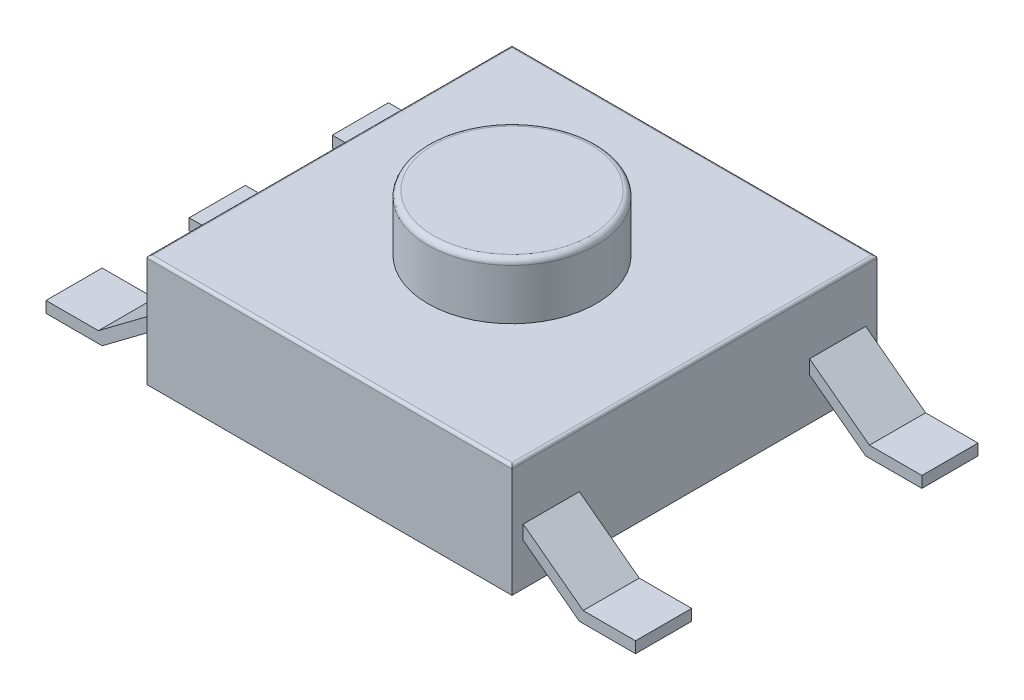
SolidWorks part; units mm, degrees
ref_plane "Front" through (0, 0, 0) normal (0, 0, 1) x (1, 0, 0)
ref_plane "Top" through (0, 0, 0) normal (0, 1, 0) x (1, 0, 0)
ref_plane "Right" through (0, 0, 0) normal (1, 0, 0) x (0, 0, -1)
sketch "Sketch1" plane through (0, 0, 0) normal (0, 1, 0) x (1, 0, 0)
  line L1 (0, 0) -> (6.5, 0)
  line L2 (0, 0) -> (0, 6.5)
  line L3 (0, 6.5) -> (6.5, 6.5)
  line L4 (6.5, 0) -> (6.5, 6.5)
  dimension "D1" = 6.5
extrude "Boss-Extrude1" add sketch "Sketch1" along normal blind 2
sketch "Sketch2" plane through (0, 2, 0) normal (0, 1, 0) x (1, 0, 0)
  line L0 (0, 0) -> (6.5, 6.5) construction
  circle A0 centre (3.25, 3.25) radius 1.5
  dimension "D1" = 3
extrude "Boss-Extrude2" add sketch "Sketch2" along normal blind 1
fillet "Fillet1" radius 0.1 1 edges at (3.25, 3, -1.75)
fillet "Fillet2" radius 0.05 4 edges at (3.25, 2, 0) (6.5, 2, -3.25) (3.25, 2, -6.5) (0, 2, -3.25)
sketch "Sketch3" plane through (0, 0, 0) normal (0, 0, 1) x (1, 0, 0)
  line L0 (6.5, 1) -> (7.5667, 0.2)
  line L1 (6.5, 1.95) -> (6.5, 0) construction
  line L2 (7.5667, 0.2) -> (8.5, 0.2)
  line L3 (8.5, 0.2) -> (8.5, 0)
  line L4 (8.5, 0) -> (7.5, 0)
  line L5 (7.5, 0) -> (6.5, 0.75)
  line L6 (3.25, 1.95) -> (3.25, 0) construction
  line L7 (6.5, 1.95) -> (0, 1.95) construction
  line L8 (0, 0) -> (6.5, 0) construction
  line L9 (-2, 0) -> (-1, 0)
  line L10 (-2, 0.2) -> (-2, 0)
  line L11 (-1.0667, 0.2) -> (-2, 0.2)
  line L12 (-1, 0) -> (0, 0.75)
  line L13 (0, 1) -> (-1.0667, 0.2)
  line L14 (0, 1) -> (0, 0.75)
  line L15 (6.5, 1) -> (6.5, 0.75)
  dimension "D1" = 0.2
  dimension "D2" = 0.2
  dimension "D3" = 2
  dimension "D4" = 1
  dimension "D5" = 1
extrude "Boss-Extrude3" add sketch "Sketch3" against normal through all
sketch "Sketch4" plane through (0, 0, 0) normal (0, -1, 0) x (-1, 0, 0)
  line L0 (2, 6.5) -> (2, 0) construction
  line L1 (2, 1.2) -> (0, 1.2)
  line L2 (2, 1.2) -> (2, 2.75)
  line L3 (2, 2.75) -> (0, 2.75)
  line L4 (0, 1.2) -> (0, 2.75)
  line L5 (0, 6.5) -> (0, 0) construction
  line L6 (-6.5, 0) -> (-6.5, 6.5) construction
  line L7 (2, 3.75) -> (0, 3.75)
  line L8 (2, 3.75) -> (2, 5.3)
  line L9 (2, 5.3) -> (0, 5.3)
  line L10 (0, 3.75) -> (0, 5.3)
  line L11 (-6.5, 1.2) -> (-8.5, 1.2)
  line L12 (-6.5, 1.2) -> (-6.5, 5.3)
  line L13 (-6.5, 5.3) -> (-8.5, 5.3)
  line L14 (-8.5, 1.2) -> (-8.5, 5.3)
  line L15 (-8.5, 6.5) -> (-8.5, 0) construction
  line L16 (0, 6.5) -> (0, 0) construction
  line L17 (2, 0) -> (0, 0)
  line L18 (2, 0) -> (2, 0.2)
  line L19 (2, 0.2) -> (0, 0.2)
  line L20 (0, 0) -> (0, 0.2)
  line L21 (2, 6.5) -> (0, 6.5)
  line L22 (2, 6.5) -> (2, 6.3)
  line L23 (2, 6.3) -> (0, 6.3)
  line L24 (0, 6.5) -> (0, 6.3)
  line L26 (-6.5, 6.5) -> (-8.5, 6.5)
  line L27 (-6.5, 6.5) -> (-6.5, 6.3)
  line L28 (-6.5, 6.3) -> (-8.5, 6.3)
  line L29 (-8.5, 6.5) -> (-8.5, 6.3)
  line L30 (-6.5, 0) -> (-8.5, 0)
  line L31 (-6.5, 0) -> (-6.5, 0.2)
  line L32 (-6.5, 0.2) -> (-8.5, 0.2)
  line L33 (-8.5, 0) -> (-8.5, 0.2)
  dimension "D1" = 0.2
  dimension "D2" = 0.2
  dimension "D3" = 0.2
  dimension "D4" = 0.2
  dimension "D5" = 1
  dimension "D6" = 1
  dimension "D7" = 1
  dimension "D8" = 1
  dimension "D9" = 1
extrude "Cut-Extrude1" cut sketch "Sketch4" against normal through all
